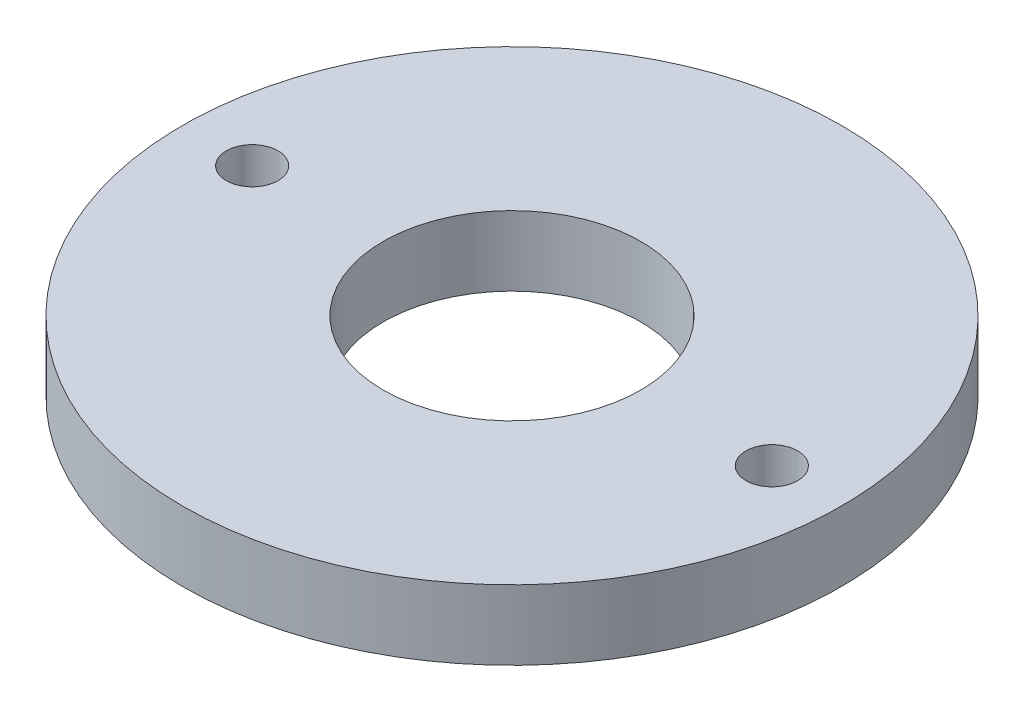
SolidWorks part; units mm, degrees
ref_plane "Front Plane" through (0, 0, 0) normal (0, 0, 1) x (1, 0, 0)
ref_plane "Top Plane" through (0, 0, 0) normal (0, 1, 0) x (1, 0, 0)
ref_plane "Right Plane" through (0, 0, 0) normal (1, 0, 0) x (0, 0, -1)
sketch "Sketch1" plane through (0, 0, 0) normal (0, 1, 0) x (1, 0, 0)
  circle A0 centre (0, 0) radius 14.65
  circle A1 centre (0, 0) radius 5.725
  circle A2 centre (0, 0) radius 11.55 construction
  circle A3 centre (11.55, 0) radius 1.15
  circle A4 centre (-11.55, 0) radius 1.15
  dimension "D1" = 29.3
  dimension "D2" = 11.45
  dimension "D3" = 2.3
  dimension "D4" = 23.1
extrude "Boss-Extrude1" add sketch "Sketch1" along normal blind 3.1
